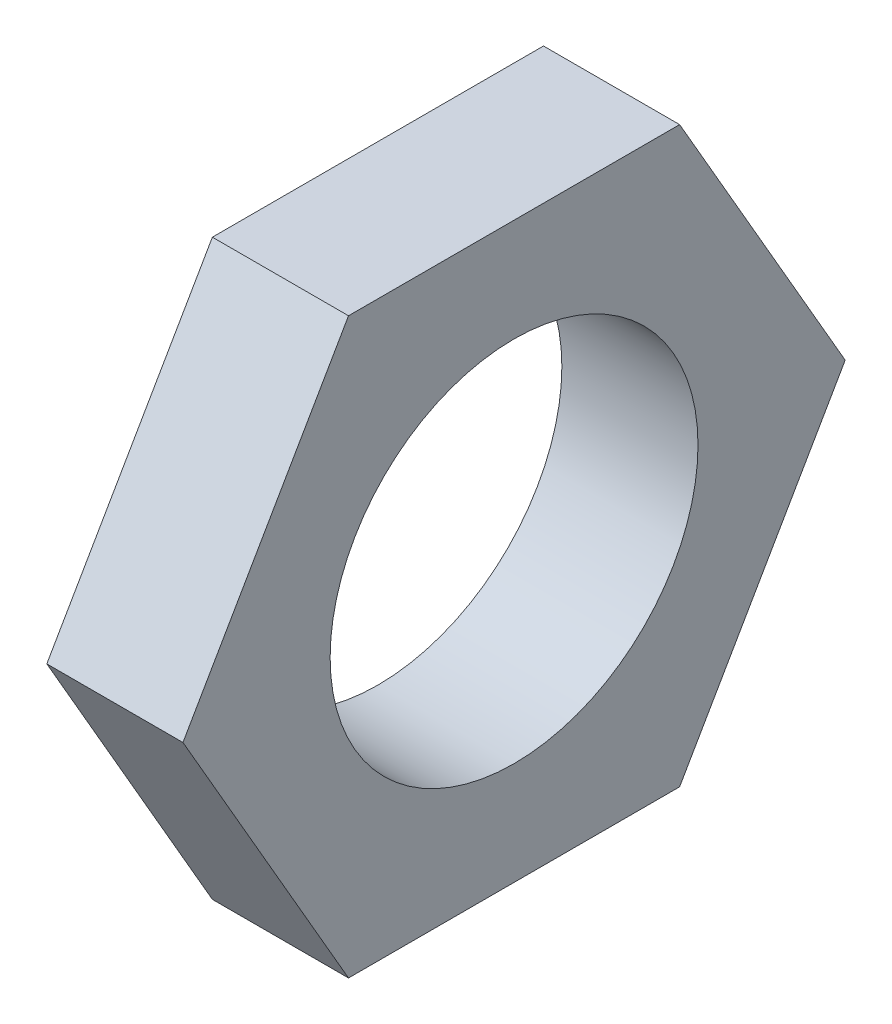
SolidWorks part; units mm, degrees
ref_plane "Front Plane" through (0, 0, 0) normal (0, 0, 1) x (1, 0, 0)
ref_plane "Top Plane" through (0, 0, 0) normal (0, 1, 0) x (1, 0, 0)
ref_plane "Right Plane" through (0, 0, 0) normal (1, 0, 0) x (0, 0, -1)
sketch "Sketch1" plane through (0, 0, 0) normal (1, 0, 0) x (0, 0, -1)
  line L1 (5.7158, 0) -> (2.8579, 4.95)
  line L2 (2.8579, 4.95) -> (-2.8579, 4.95)
  line L3 (-2.8579, 4.95) -> (-5.7158, 0)
  line L4 (-5.7158, 0) -> (-2.8579, -4.95)
  line L5 (-2.8579, -4.95) -> (2.8579, -4.95)
  line L6 (2.8579, -4.95) -> (5.7158, 0)
  circle A0 centre (0, 0) radius 4.95 construction
  circle A1 centre (0, 0) radius 3.175
  dimension "D2" = 6.35
  dimension "D1" = 9.9
extrude "Boss-Extrude1" add sketch "Sketch1" along normal blind 2.35
